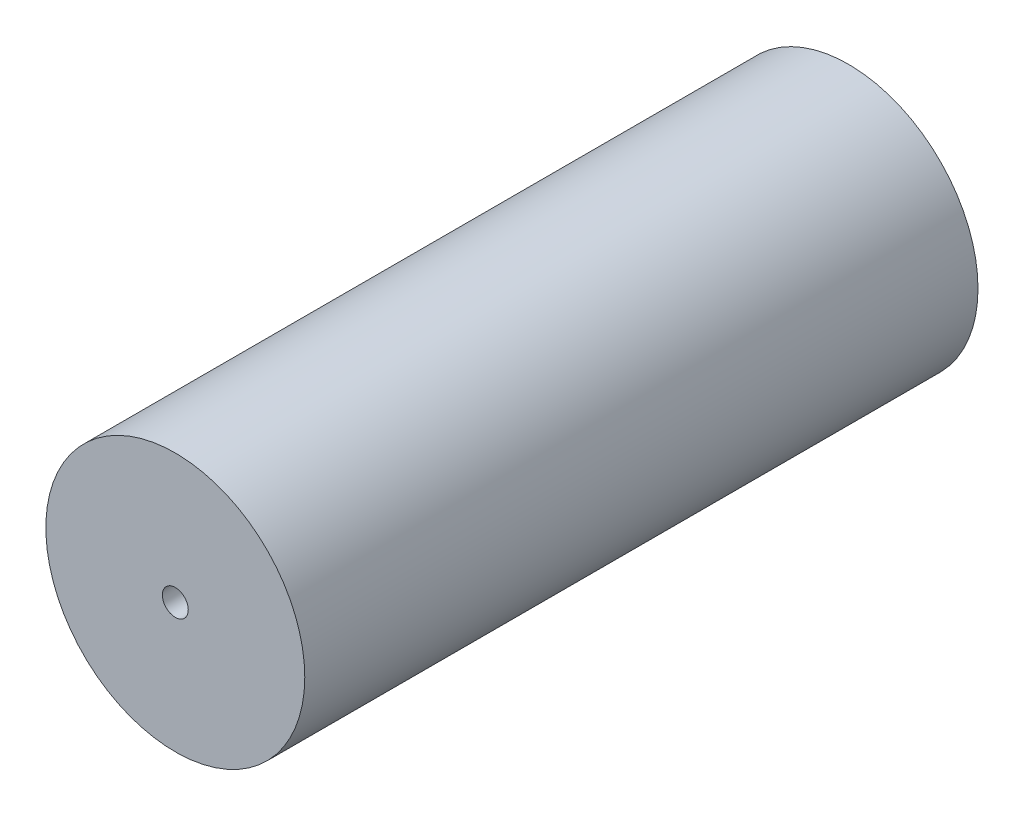
SolidWorks part; units mm, degrees
ref_plane "Front Plane" through (0, 0, 0) normal (0, 0, 1) x (1, 0, 0)
ref_plane "Top Plane" through (0, 0, 0) normal (0, 1, 0) x (1, 0, 0)
ref_plane "Right Plane" through (0, 0, 0) normal (1, 0, 0) x (0, 0, -1)
sketch "Sketch1" plane through (0, 0, 0) normal (0, 0, 1) x (1, 0, 0)
  circle A0 centre (0, 0) radius 5
  circle A1 centre (0, 0) radius 0.5
  dimension "D1" = 10
  dimension "D2" = 1
extrude "Boss-Extrude1" add sketch "Sketch1" along normal blind 26
